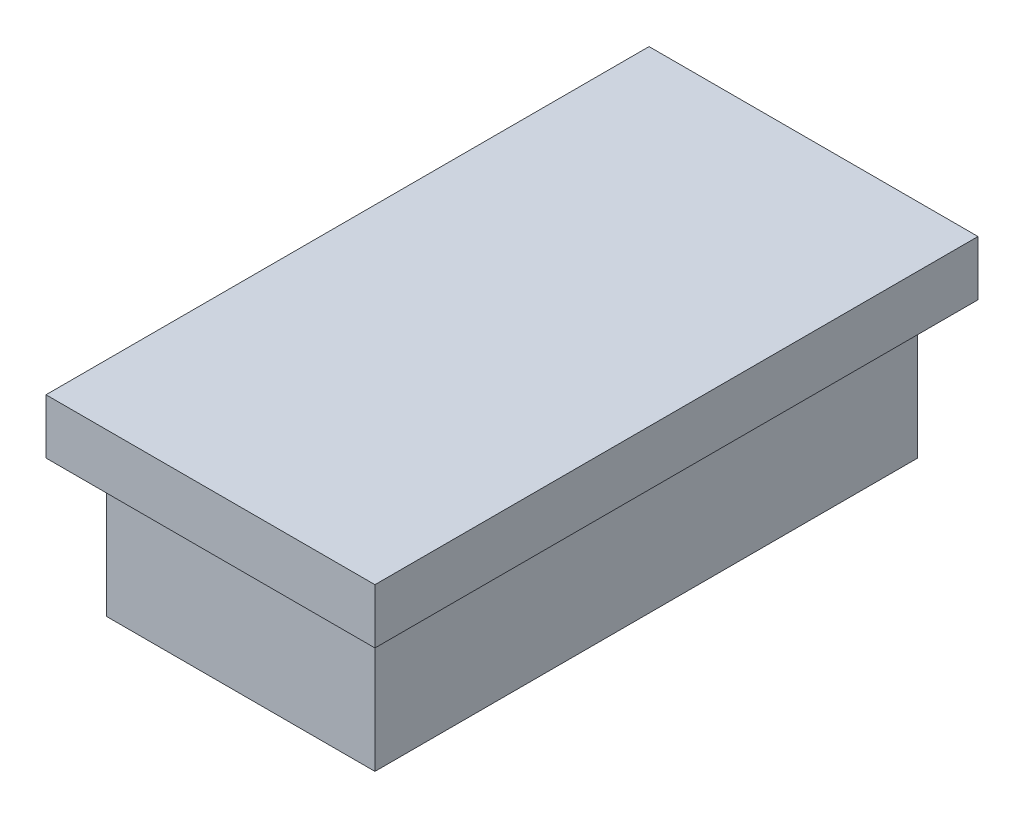
SolidWorks part; units mm, degrees
ref_plane "Спереди" through (0, 0, 0) normal (0, 0, 1) x (1, 0, 0)
ref_plane "Сверху" through (0, 0, 0) normal (0, 1, 0) x (1, 0, 0)
ref_plane "Справа" through (0, 0, 0) normal (1, 0, 0) x (0, 0, -1)
sketch "Sketch1" plane through (0, 0, 0) normal (0, 1, 0) x (1, 0, 0)
  line L1 (4.9, -9.9) -> (-4.9, -9.9)
  line L2 (4.9, -9.9) -> (4.9, 9.9)
  line L3 (4.9, 9.9) -> (-4.9, 9.9)
  line L4 (-4.9, -9.9) -> (-4.9, 9.9)
  line L5 (4.9, -9.9) -> (-4.9, 9.9) construction
  line L6 (4.9, 9.9) -> (-4.9, -9.9) construction
  point P0 (0, 0)
  dimension "D1" = 9.8
  dimension "D2" = 19.8
extrude "Boss-Extrude1" add sketch "Sketch1" along normal blind 5
sketch "Sketch2" plane through (0, 5, 0) normal (0, 1, 0) x (1, 0, 0)
  line L0 (-4.9, 9.9) -> (4.9, -9.9) construction
  line L1 (0, 11) -> (0, -11) construction
  line L2 (6, -11) -> (-6, -11)
  line L3 (6, -11) -> (6, 11)
  line L4 (6, 11) -> (-6, 11)
  line L5 (-6, -11) -> (-6, 11)
  line L6 (6, -11) -> (-6, 11) construction
  line L7 (6, 11) -> (-6, -11) construction
  point P4 (0, 0)
  dimension "D1" = 12
  dimension "D2" = 22
extrude "Boss-Extrude2" add sketch "Sketch2" along normal blind 2
